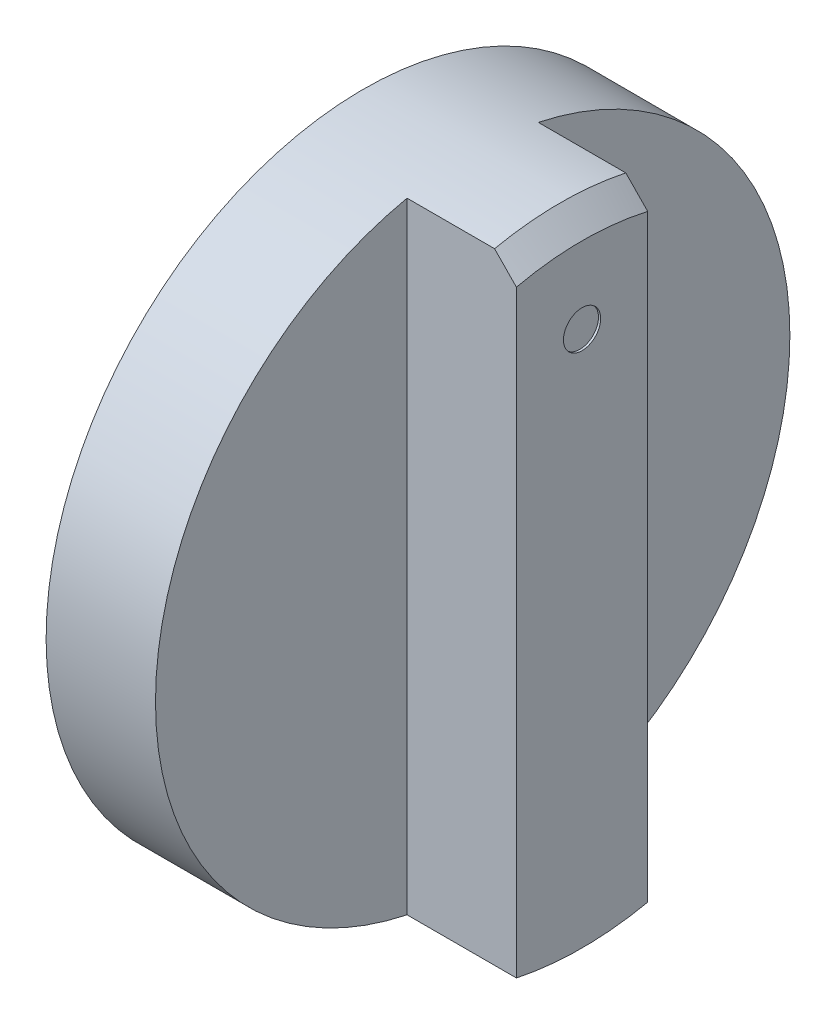
SolidWorks part; units mm, degrees
ref_plane "前视" through (0, 0, 0) normal (0, 0, 1) x (1, 0, 0)
ref_plane "上视" through (0, 0, 0) normal (0, 1, 0) x (1, 0, 0)
ref_plane "右视" through (0, 0, 0) normal (1, 0, 0) x (0, 0, -1)
sketch "草图1" plane through (0, 0, 0) normal (1, 0, 0) x (0, 0, -1)
  circle A0 centre (0, 0) radius 14.5
  dimension "D1" = 29
extrude "凸台-拉伸1" add sketch "草图1" along normal blind 5
sketch "草图2" plane through (5, 0, 0) normal (1, 0, 0) x (0, 0, -1)
  line L1 (-3, 14.5) -> (3, 14.5)
  line L2 (-3, 14.5) -> (-3, -14.5)
  line L3 (-3, -14.5) -> (3, -14.5)
  line L4 (3, 14.5) -> (3, -14.5)
  line L5 (-3, 14.5) -> (3, -14.5) construction
  line L6 (-3, -14.5) -> (3, 14.5) construction
  circle A0 centre (0, 0) radius 14.5 construction
  arc A1 (3, 14.1863) -> (-3, 14.1863) centre (0, 0) ccw
  arc A2 (-3, -14.1863) -> (3, -14.1863) centre (0, 0) ccw
  point P0 (0, 0)
  circle M1 centre (0, 0) radius 14.5
  dimension "D1" = 6
extrude "凸台-拉伸2" add sketch "草图2" along normal blind 5 contours L4 L2 M1
chamfer "倒角1" distance 1 angle 45 1 edges at (10, 14.5, 0)
sketch "草图3" plane through (10, 0, 0) normal (1, 0, 0) x (0, 0, -1)
  line L0 (0, 10) -> (0, 0) construction
  circle A0 centre (0, 10) radius 0.85
  dimension "D1" = 1.7
  dimension "D2" = 10
extrude "切除-拉伸1" cut sketch "草图3" against normal blind 0.1
